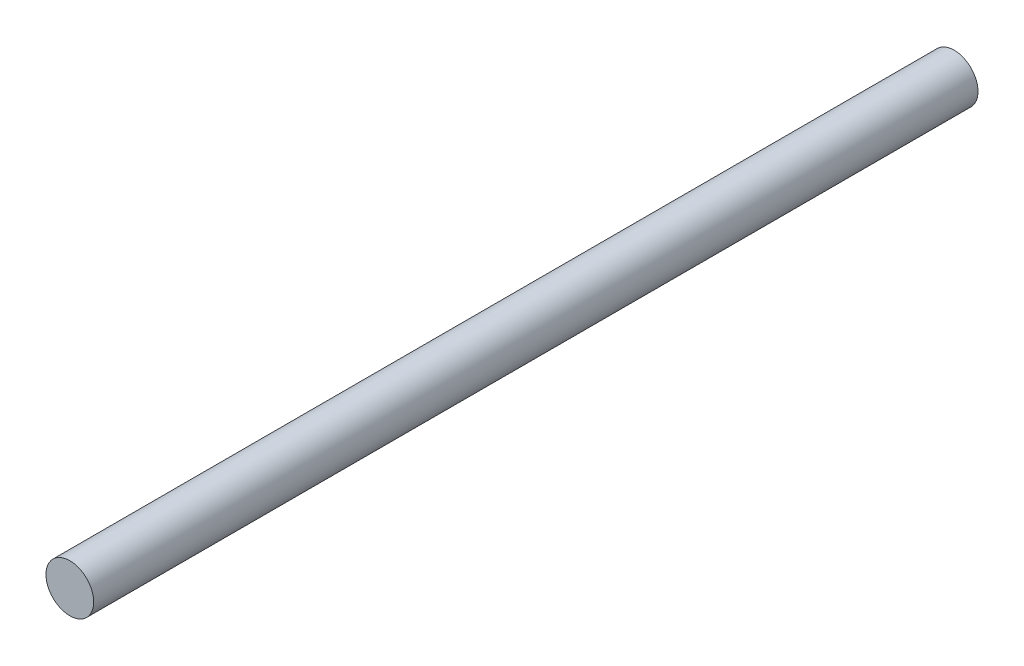
SolidWorks part; units mm, degrees
ref_plane "Front Plane" through (0, 0, 0) normal (0, 0, 1) x (1, 0, 0)
ref_plane "Top Plane" through (0, 0, 0) normal (0, 1, 0) x (1, 0, 0)
ref_plane "Right Plane" through (0, 0, 0) normal (1, 0, 0) x (0, 0, -1)
sketch "Sketch1" plane through (0, 0, 0) normal (0, 0, 1) x (1, 0, 0)
  circle A0 centre (0, 0) radius 9.4488
  dimension "D1" = 18.8976
extrude "Boss-Extrude1" add sketch "Sketch1" along normal blind 350
